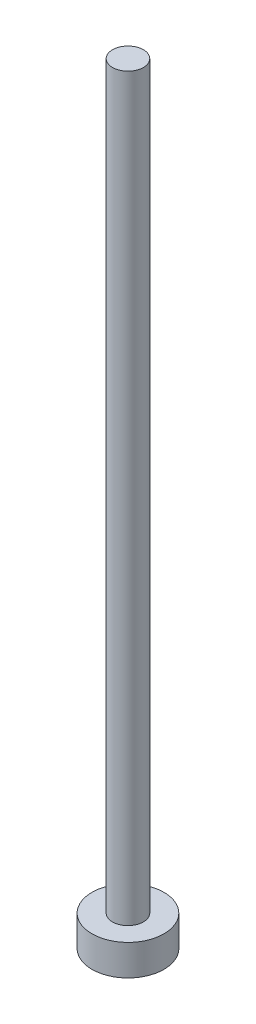
SolidWorks part; units mm, degrees
ref_plane "前视基准面" through (0, 0, 0) normal (0, 0, 1) x (1, 0, 0)
ref_plane "上视基准面" through (0, 0, 0) normal (0, 1, 0) x (1, 0, 0)
ref_plane "右视基准面" through (0, 0, 0) normal (1, 0, 0) x (0, 0, -1)
sketch "草图1" plane through (0, 0, 0) normal (0, 0, 1) x (1, 0, 0)
  line L0 (0, 78.7628) -> (0, -6.3129) construction
  line L1 (1.5, 70) -> (1.5, 72)
  line L2 (1.5, 70) -> (1.5, 0)
  line L3 (1.5, 0) -> (3.5, 0)
  line L4 (3.5, 0) -> (3.5, -3)
  line L5 (3.5, -3) -> (0, -3)
  line L6 (0, 70) -> (0, -3)
  line L7 (1.5, 72) -> (0, 72)
  line L9 (0, 72) -> (0, 70)
revolve "旋转1" add sketch "草图1" angle 360 about L0
sketch "草图2" plane through (0, -3, 0) normal (0, -1, 0) x (1, 0, 0)
  line L1 (2.504, 0) -> (1.252, 2.1685)
  line L2 (1.252, 2.1685) -> (-1.252, 2.1685)
  line L3 (-1.252, 2.1685) -> (-2.504, 0)
  line L4 (-2.504, 0) -> (-1.252, -2.1685)
  line L5 (-1.252, -2.1685) -> (1.252, -2.1685)
  line L6 (1.252, -2.1685) -> (2.504, 0)
  circle A0 centre (0, 0) radius 2.1685 construction
extrude "切除-拉伸1" cut sketch "草图2" against normal blind 2
scale "缩放比例1" scale about centroid uniform scaling yes scale factor 0.58
move or copy body "实体-移动/复制1" [suppressed] bodies to move or copy 107
